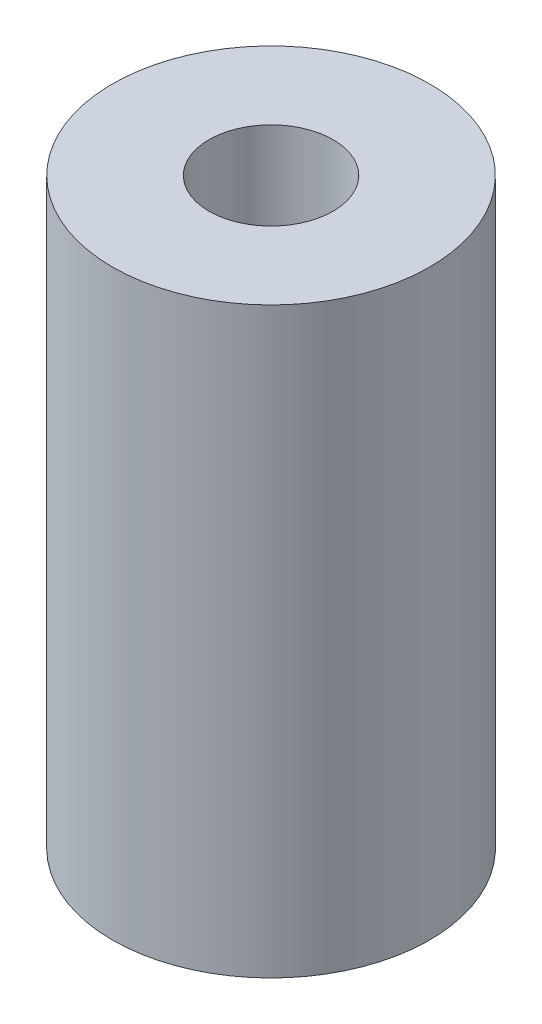
SolidWorks part; units mm, degrees
material "Bambu PAHT-CF"
ref_plane "Front Plane" through (0, 0, 0) normal (0, 0, 1) x (1, 0, 0)
ref_plane "Top Plane" through (0, 0, 0) normal (0, 1, 0) x (1, 0, 0)
ref_plane "Right Plane" through (0, 0, 0) normal (1, 0, 0) x (0, 0, -1)
sketch "Sketch2" plane through (0, 0, 0) normal (0, 1, 0) x (1, 0, 0)
  circle A0 centre (0, 0) radius 3.7258
  circle A1 centre (0, 0) radius 9.525
  dimension "D1" = 7.4516
  dimension "D2" = 19.05
extrude "Boss-Extrude1" add sketch "Sketch2" along normal blind 35
